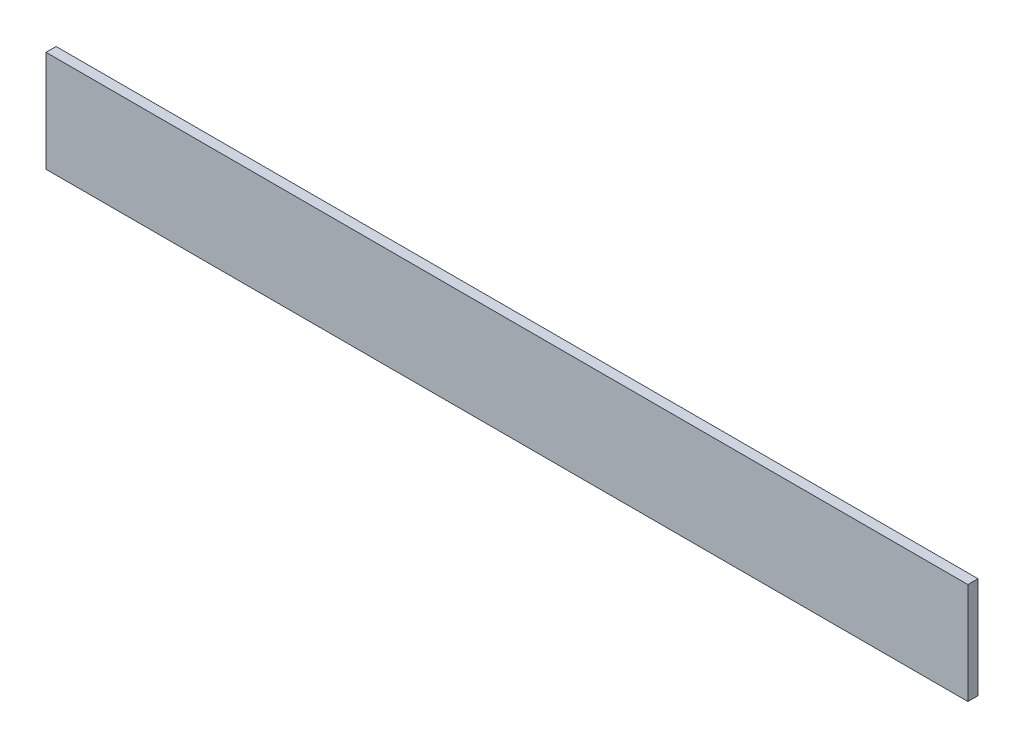
SolidWorks part; units mm, degrees
ref_plane "Plan de face" through (0, 0, 0) normal (0, 0, 1) x (1, 0, 0)
ref_plane "Plan de dessus" through (0, 0, 0) normal (0, 1, 0) x (1, 0, 0)
ref_plane "Plan de droite" through (0, 0, 0) normal (1, 0, 0) x (0, 0, -1)
sketch "Esquisse1" plane through (0, 0, 0) normal (0, 0, 1) x (1, 0, 0)
  line L1 (-256.3208, 10.4708) -> (16.6792, 10.4708)
  line L2 (-256.3208, 10.4708) -> (-256.3208, -19.5292)
  line L3 (-256.3208, -19.5292) -> (16.6792, -19.5292)
  line L4 (16.6792, 10.4708) -> (16.6792, -19.5292)
  dimension "D1" = 30
  dimension "D2" = 273
extrude "Boss.-Extru.1" add sketch "Esquisse1" along normal blind 3
equation "\"EpaisseurPlaque\"= 3"
equation "\"ProfondeurBoite\"=460"
equation "\"LongueurSyphon\"=270"
equation "\"LargeurSyphon\"=120"
equation "\"HauteurCoteDroit\"= 490"
equation "\"HauteurCoteGauche\"= 540"
equation "\"HauteurSolSyphon\"= 300"
equation "\"HauteurSyphon\"=\"HauteurCoteGauche\"-\"HauteurSolSyphon\""
equation "\"LargeurDroite\"=10"
equation "\"LargeurGauche\"=150"
equation "\"LargeurBoite\"= \"LargeurDroite\" + \"LargeurGauche\" + \"LargeurSyphon\""
equation "\"HauteurBagueSyphon\"=50"
equation "\"D2@Esquisse1\"=\"LongueurSyphon\" +\"EpaisseurPlaque\""
